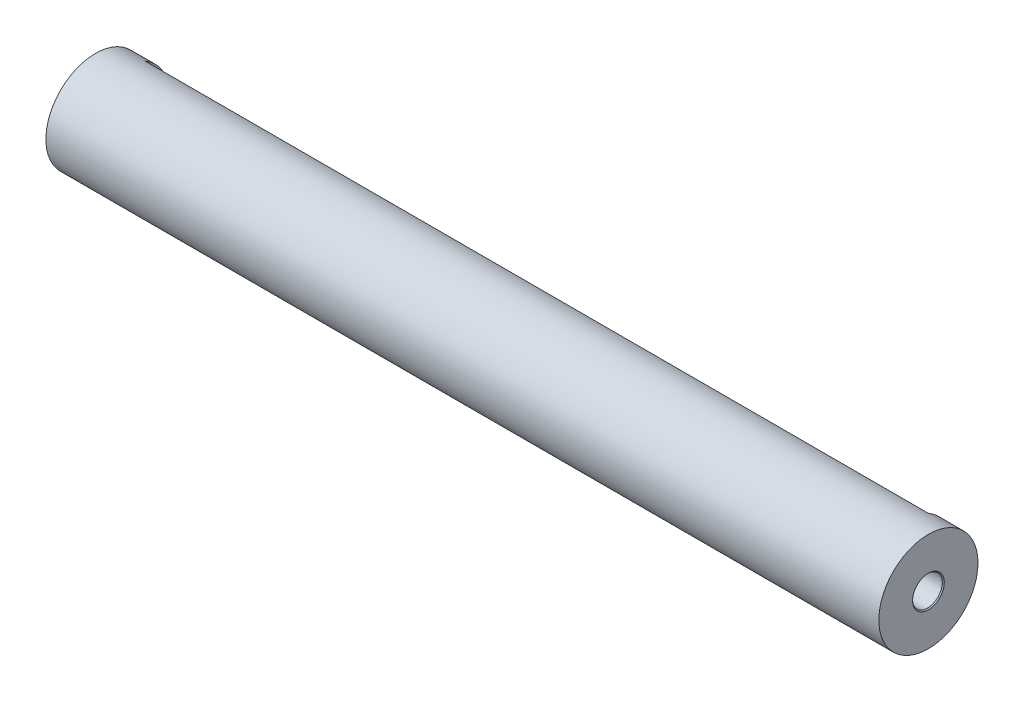
SolidWorks part; units mm, degrees
material "2024-T4"
ref_plane "Front" through (0, 0, 0) normal (0, 0, 1) x (1, 0, 0)
ref_plane "Top" through (0, 0, 0) normal (0, 1, 0) x (1, 0, 0)
ref_plane "Right" through (0, 0, 0) normal (1, 0, 0) x (0, 0, -1)
sketch "Эскиз1" plane through (0, 0, 0) normal (1, 0, 0) x (0, 0, -1)
  circle A0 centre (0, 0) radius 5
  dimension "D1" = 10
extrude "Бобышка-Вытянуть1" add sketch "Эскиз1" along normal blind 84
hole_wizard "Отверстие обработанное метчиком M31" positions "Эскиз3" profile "Эскиз2" tap size "M3" standard "DIN"
sketch "Эскиз3" plane through (0, 0, 0) normal (-1, 0, 0) x (0, 0, 1)
  point P0 (0, 0)
sketch "Эскиз2" plane through (0, 0, 0) normal (0, 1, 0) x (0, 0, 1)
  line L0 (0, 0) -> (0, 12.7511)
  line L1 (0, 12.7511) -> (1.25, 12)
  line L2 (1.25, 12) -> (1.25, 9)
  line L3 (1.25, 9) -> (1.5, 9)
  line L5 (1.5, 9) -> (1.5, 0.1)
  line L6 (1.5, 0.1) -> (1.6, 0)
  line L7 (1.6, 0) -> (0, 0)
  line L8 (-1.5, 0.1) -> (-1.6, 0) construction
  line L10 (0, 12.7511) -> (-1.25, 12) construction
  line L11 (0, -6.35) -> (0, 107.95) construction
  dimension "Диаметр сверла" = 2.5
  dimension "Глубина сверла" = 12
  dimension "Диаметр резьбы" = 3
  dimension "Глубина резьбы" = 9
  dimension "Диаметр передней зенковки" = 3.2
  dimension "Угол передней зенковки" = 90
  dimension "Угол заточки сверла" = 118
hole_wizard "Отверстие обработанное метчиком M32" positions "Эскиз5" profile "Эскиз4" tap size "M3" standard "DIN"
sketch "Эскиз5" plane through (84, 0, 0) normal (1, 0, 0) x (0, 0, -1)
  point P0 (0, 0)
sketch "Эскиз4" plane through (84, 0, 0) normal (0, 1, 0) x (0, 0, -1)
  line L0 (0, 0) -> (0, 12.7511)
  line L1 (0, 12.7511) -> (1.25, 12)
  line L2 (1.25, 12) -> (1.25, 9)
  line L3 (1.25, 9) -> (1.5, 9)
  line L5 (1.5, 9) -> (1.5, 0.1)
  line L6 (1.5, 0.1) -> (1.6, 0)
  line L7 (1.6, 0) -> (0, 0)
  line L8 (-1.5, 0.1) -> (-1.6, 0) construction
  line L10 (0, 12.7511) -> (-1.25, 12) construction
  line L11 (0, -6.35) -> (0, 107.95) construction
  dimension "Диаметр сверла" = 2.5
  dimension "Глубина сверла" = 12
  dimension "Диаметр резьбы" = 3
  dimension "Глубина резьбы" = 9
  dimension "Диаметр передней зенковки" = 3.2
  dimension "Угол передней зенковки" = 90
  dimension "Угол заточки сверла" = 118
sketch "Эскиз6" plane through (0, 0, 0) normal (0, 1, 0) x (1, 0, 0)
  line L0 (84, -5) -> (84, 5) construction
  line L1 (2.5, 11.2523) -> (81.5, 11.2523)
  line L2 (2.5, 11.2523) -> (2.5, 2.5)
  line L3 (2.5, 2.5) -> (81.5, 2.5)
  line L4 (81.5, 11.2523) -> (81.5, 2.5)
  line L5 (0, 5) -> (0, -5) construction
  dimension "D1" = 2.5
  dimension "D2" = 2.5
  dimension "D3" = 2.5
extrude "Вырез-Вытянуть1" cut sketch "Эскиз6" against normal through all and the other way through all contours L4 L1 L2 L3
